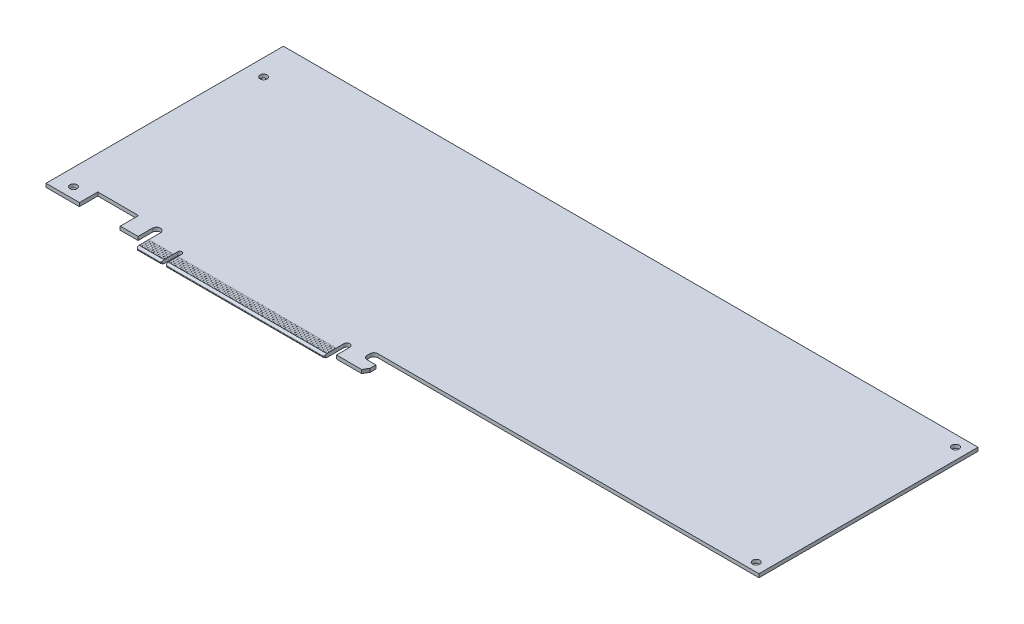
SolidWorks part; units mm, degrees
ref_plane "Front Plane" through (0, 0, 0) normal (0, 0, 1) x (1, 0, 0)
ref_plane "Top Plane" through (0, 0, 0) normal (0, 1, 0) x (1, 0, 0)
ref_plane "Right Plane" through (0, 0, 0) normal (1, 0, 0) x (0, 0, -1)
sketch "Sketch1" plane through (0, 0, 0) normal (0, 1, 0) x (1, 0, 0)
  line L1 (0, 0) -> (312, 0)
  line L2 (0, 0) -> (0, 111.15)
  line L3 (0, 111.15) -> (312, 111.15)
  line L4 (312, 0) -> (312, 111.15)
  dimension "D1" = 312
  dimension "D2" = 111.15
extrude "Boss-Extrude1" add sketch "Sketch1" against normal blind 1.6
sketch "Sketch2" plane through (0, 0, 0) normal (0, 1, 0) x (1, 0, 0)
  line L0 (0, 4.5) -> (15, 4.5)
  line L1 (0, 111.15) -> (0, 0) construction
  line L2 (15, 4.5) -> (15, 12.75)
  line L3 (15, 12.75) -> (33.35, 12.75)
  line L4 (33.35, 12.75) -> (33.35, 4.5)
  line L5 (33.35, 4.5) -> (41.35, 4.5)
  line L6 (41.35, 4.5) -> (41.35, 10.925)
  line L7 (15, 4.5) -> (33.35, 4.5) construction
  line L8 (45, 10.925) -> (45, 0)
  line L9 (0, 0) -> (312, 0) construction
  line L10 (45, 0) -> (0, 0)
  line L11 (0, 0) -> (0, 4.5)
  line L12 (33.35, 12.75) -> (43.175, 12.75) construction
  line L13 (56.2, 0) -> (56.2, 7.45)
  line L14 (312, 12.75) -> (312, 0)
  line L15 (58.1, 7.45) -> (58.1, 0)
  line L16 (58.1, 0) -> (56.2, 0)
  line L17 (129.3, 0) -> (129.3, 12.75)
  line L18 (129.3, 12.75) -> (312, 12.75)
  line L19 (312, 0) -> (312, 111.15) construction
  line L20 (43.175, 12.75) -> (129.3, 12.75) construction
  line L21 (312, 0) -> (129.3, 0)
  line L22 (57.15, 0) -> (57.15, -8.3018) construction
  arc A0 (41.35, 10.925) -> (45, 10.925) centre (43.175, 10.925) cw
  arc A1 (56.2, 7.45) -> (58.1, 7.45) centre (57.15, 7.45) cw
  point P16 (33.35, 8.625)
  point P32 (57.15, 8.4)
  dimension "D1" = 1.825
  dimension "D6" = 0.95
  dimension "D2" = 8.25
  dimension "D3" = 11.65
  dimension "D4" = 15
  dimension "D5" = 4.5
  dimension "D7" = 12.15
  dimension "D8" = 8.4
  dimension "D9" = 57.15
  dimension "D10" = 72.15
extrude "Cut-Extrude1" cut sketch "Sketch2" against normal up to next
sketch "Sketch3" plane through (0, 0, 0) normal (0, 1, 0) x (1, 0, 0)
  line L0 (45, 0) -> (56.2, 0) construction
  line L1 (45.25, 1.4) -> (45.95, 1.4)
  line L2 (45.25, 1.4) -> (45.25, 5.6)
  line L3 (45.25, 5.6) -> (45.95, 5.6)
  line L4 (45.95, 1.4) -> (45.95, 5.6)
  line L5 (45, 0) -> (45, 10.925) construction
  line L6 (46.25, 1.4) -> (46.95, 1.4)
  line L7 (46.25, 1.4) -> (46.25, 5.6)
  line L8 (46.25, 5.6) -> (46.95, 5.6)
  line L9 (46.95, 1.4) -> (46.95, 5.6)
  line L10 (47.25, 1.4) -> (47.95, 1.4)
  line L11 (47.25, 1.4) -> (47.25, 5.6)
  line L12 (47.25, 5.6) -> (47.95, 5.6)
  line L13 (47.95, 1.4) -> (47.95, 5.6)
  line L14 (48.25, 1.4) -> (48.95, 1.4)
  line L15 (48.25, 1.4) -> (48.25, 5.6)
  line L16 (48.25, 5.6) -> (48.95, 5.6)
  line L17 (48.95, 1.4) -> (48.95, 5.6)
  line L18 (49.25, 1.4) -> (49.95, 1.4)
  line L19 (49.25, 1.4) -> (49.25, 5.6)
  line L20 (49.25, 5.6) -> (49.95, 5.6)
  line L21 (49.95, 1.4) -> (49.95, 5.6)
  line L22 (50.25, 1.4) -> (50.95, 1.4)
  line L23 (50.25, 1.4) -> (50.25, 5.6)
  line L24 (50.25, 5.6) -> (50.95, 5.6)
  line L25 (50.95, 1.4) -> (50.95, 5.6)
  line L26 (51.25, 1.4) -> (51.95, 1.4)
  line L27 (51.25, 1.4) -> (51.25, 5.6)
  line L28 (51.25, 5.6) -> (51.95, 5.6)
  line L29 (51.95, 1.4) -> (51.95, 5.6)
  line L30 (52.25, 1.4) -> (52.95, 1.4)
  line L31 (52.25, 1.4) -> (52.25, 5.6)
  line L32 (52.25, 5.6) -> (52.95, 5.6)
  line L33 (52.95, 1.4) -> (52.95, 5.6)
  line L34 (53.25, 1.4) -> (53.95, 1.4)
  line L35 (53.25, 1.4) -> (53.25, 5.6)
  line L36 (53.25, 5.6) -> (53.95, 5.6)
  line L37 (53.95, 1.4) -> (53.95, 5.6)
  line L38 (54.25, 1.4) -> (54.95, 1.4)
  line L39 (54.25, 1.4) -> (54.25, 5.6)
  line L40 (54.25, 5.6) -> (54.95, 5.6)
  line L41 (54.95, 1.4) -> (54.95, 5.6)
  line L42 (55.25, 1.4) -> (55.95, 1.4)
  line L43 (55.25, 1.4) -> (55.25, 5.6)
  line L44 (55.25, 5.6) -> (55.95, 5.6)
  line L45 (55.95, 1.4) -> (55.95, 5.6)
  dimension "D1" = 1.4
  dimension "D2" = 0.7
  dimension "D3" = 5.6
  dimension "D4" = 0.25
  dimension "D5" = 11
extrude "Boss-Extrude2" add sketch "Sketch3" along normal blind 0.035 and the other way blind 1.635 separate body
sketch "Sketch4" plane through (0, 0, 0) normal (0, 1, 0) x (1, 0, 0)
  line L0 (58.1, 0) -> (129.3, 0) construction
  line L1 (58.35, 1.4) -> (59.05, 1.4)
  line L2 (58.35, 1.4) -> (58.35, 5.6)
  line L3 (58.35, 5.6) -> (59.05, 5.6)
  line L4 (59.05, 1.4) -> (59.05, 5.6)
  line L5 (58.1, 0) -> (58.1, 7.45) construction
  dimension "D1" = 0.7
  dimension "D2" = 1.4
  dimension "D3" = 5.6
  dimension "D4" = 0.25
extrude "Boss-Extrude3" add sketch "Sketch4" along normal blind 0.035 and the other way blind 1.635 separate body
pattern_linear "LPattern1" count 71 spacing 1 along (1, 0, 0)
hole_wizard "1/8 (0.125) Diameter Hole1" positions "Sketch5" profile "Sketch6" hole size "1/8" standard "ANSI Inch" end condition up to next
sketch "Sketch5" plane through (0, 0, 0) normal (0, 1, 0) x (1, 0, 0)
  line L0 (15, 4.5) -> (0, 4.5) construction
  line L1 (7.5, 9.35) -> (7.5, 94.75) construction
  arc A0 (58.1, 7.45) -> (56.2, 7.45) centre (57.15, 7.45) ccw construction
  point P0 (7.5, 9.35)
  point P2 (7.5, 94.75)
  point P13 (57.15, 8.4)
  dimension "D1" = 85.4
  dimension "D2" = 4.85
  dimension "D3" = 49.65
sketch "Sketch6" plane through (7.5, 0, -9.35) normal (1, 0, 0) x (0, 0, 1)
  line L0 (0, 0) -> (0, 1.6)
  line L1 (0, 1.6) -> (1.5875, 1.6)
  line L2 (1.5875, 1.6) -> (1.5875, 0)
  line L5 (1.5875, 0) -> (0, 0)
  line L11 (0, -6.35) -> (0, 107.95) construction
  dimension "Thru Hole Dia." = 3.175
  dimension "Thru Hole Depth" = 1.6
hole_wizard "1/8 (0.125) Diameter Hole2" positions "Sketch7" profile "Sketch8" hole size "1/8" standard "ANSI Inch" end condition up to next
sketch "Sketch7" plane through (0, 0, 0) normal (0, 1, 0) x (1, 0, 0)
  line L0 (306.92, 106.13) -> (306.92, 16.6) construction
  line L2 (312, 12.75) -> (312, 111.15) construction
  line L3 (312, 12.75) -> (129.3, 12.75) construction
  point P0 (306.92, 16.6)
  point P2 (306.92, 106.13)
  dimension "D1" = 5.08
  dimension "D2" = 3.85
  dimension "D3" = 89.53
sketch "Sketch8" plane through (306.92, 0, -16.6) normal (1, 0, 0) x (0, 0, 1)
  line L0 (0, 0) -> (0, 1.601)
  line L1 (0, 1.601) -> (1.5875, 1.601)
  line L2 (1.5875, 1.601) -> (1.5875, 0)
  line L5 (1.5875, 0) -> (0, 0)
  line L11 (0, -6.35) -> (0, 107.95) construction
  dimension "Thru Hole Dia." = 3.175
  dimension "Thru Hole Depth" = 1.601
chamfer "Chamfer2" distance 0.5 angle 45 4 edges at (129.3, -0.8, 0) (58.1, -0.8, 0) (56.2, -0.8, 0) (45, -0.8, 0)
hole_wizard "1/8 (0.125) Diameter Hole3" positions "Sketch9" profile "Sketch10" hole size "1/8" standard "ANSI Inch"
sketch "Sketch9" plane through (0, 0, 0) normal (0, 1, 0) x (1, 0, 0)
  line L0 (7.5, 9.35) -> (7.5, 63.25) construction
  line L2 (15, 4.5) -> (0, 4.5) construction
  arc A0 (58.1, 7.45) -> (56.2, 7.45) centre (57.15, 7.45) ccw construction
  point P0 (7.5, 9.35)
  point P2 (7.5, 63.25)
  point P13 (57.15, 8.4)
  dimension "D1" = 53.9
  dimension "D2" = 4.85
  dimension "D3" = 49.65
sketch "Sketch10" plane through (7.5, 0, -9.35) normal (1, 0, 0) x (0, 0, 1)
  line L0 (0, 0) -> (0, 1.6)
  line L1 (0, 1.6) -> (1.5875, 1.6)
  line L2 (1.5875, 1.6) -> (1.5875, 0)
  line L5 (1.5875, 0) -> (0, 0)
  line L11 (0, -6.35) -> (0, 107.95) construction
  dimension "Thru Hole Dia." = 3.175
  dimension "Thru Hole Depth" = 1.6
sketch "Sketch11" plane through (0, 0, 0) normal (0, 1, 0) x (1, 0, 0)
  line L0 (139.05, 12.75) -> (139.05, 7.95) construction
  line L1 (312, 12.75) -> (129.3, 12.75) construction
  line L2 (139.05, 7.95) -> (144.75, 7.95)
  line L3 (144.75, 7.95) -> (144.75, 5.3749)
  line L4 (144.75, 5.3749) -> (143.35, 2.95)
  line L5 (143.35, 2.95) -> (132.05, 2.95)
  line L6 (132.05, 2.95) -> (132.05, 8.98)
  line L7 (129.3, 12.75) -> (129.3, 0.5) construction
  line L8 (129.3, 12.75) -> (129.3, 8.98)
  line L9 (129.3, 12.75) -> (139.05, 12.75)
  line L10 (143.35, 2.95) -> (145.4438, 2.95) construction
  line L11 (139.05, 9.7) -> (139.05, 11)
  line L12 (58.6, 0) -> (128.8, 0) construction
  line L13 (139.05, 12.75) -> (140.8, 12.75)
  arc A0 (58.1, 7.45) -> (56.2, 7.45) centre (57.15, 7.45) ccw construction
  arc A1 (132.05, 8.98) -> (129.3, 8.98) centre (130.675, 8.98) ccw
  arc A2 (139.05, 11) -> (140.8, 12.75) centre (140.8, 11) cw
  arc A3 (140.8, 7.95) -> (139.05, 9.7) centre (140.8, 9.7) cw
  point P12 (57.15, 8.4)
  dimension "D2" = 74.9
  dimension "D4" = 1.75
  dimension "D5" = 1.75
  dimension "D9" = 8.98
  dimension "D1" = 4.8
  dimension "D3" = 81.9
  dimension "D6" = 60
  dimension "D7" = 1.4
  dimension "D8" = 9.8
  dimension "D10" = 12.7
extrude "Boss-Extrude4" add sketch "Sketch11" against normal up to surface (1.6 mm away) up to face at (306.92, -1.6, -18.1875)
chamfer "Chamfer3" distance 0.6 distance2 1.3 2 edges at (93.7, 0, 0) (50.6, 0, 0)
chamfer "Chamfer5" distance 1.3 distance2 0.6 2 edges at (93.7, -1.6, 0) (50.6, -1.6, 0)
fillet "Fillet2" radius 0.2 4 edges at (50.6, -1, 0) (93.7, -1, 0) (93.7, -0.6, 0) (50.6, -0.6, 0)
